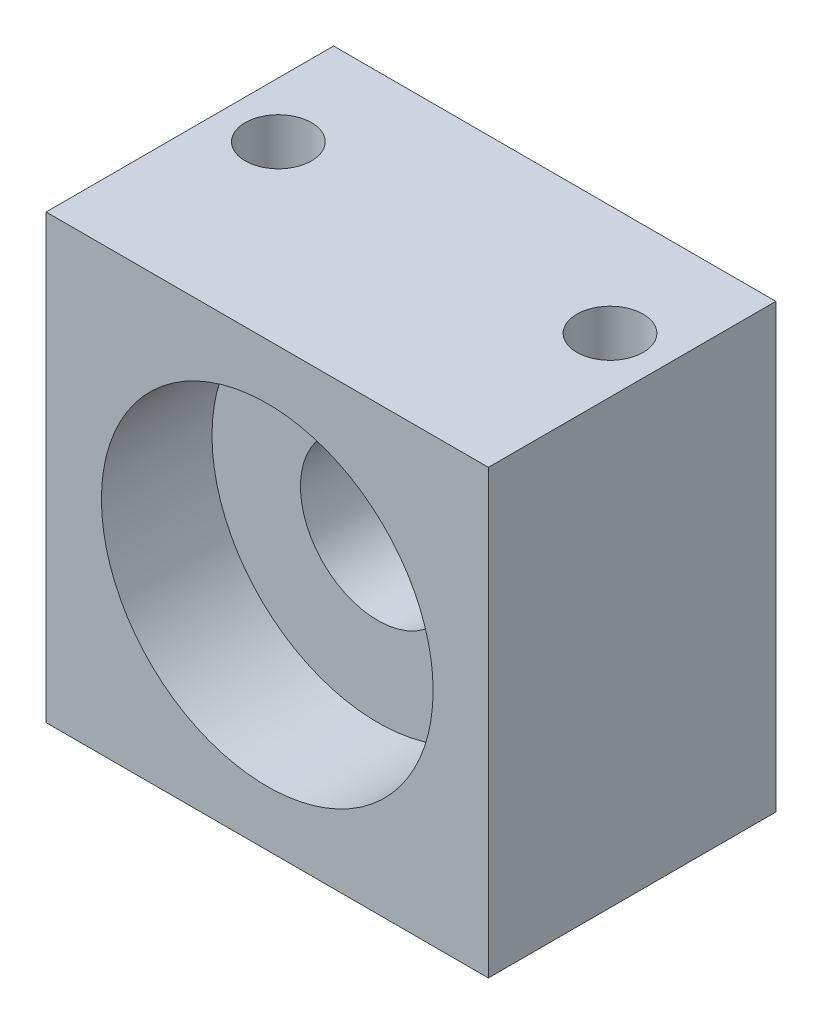
SolidWorks part; units mm, degrees
ref_plane "Front" through (0, 0, 0) normal (0, 0, 1) x (1, 0, 0)
ref_plane "Top" through (0, 0, 0) normal (0, 1, 0) x (1, 0, 0)
ref_plane "Right" through (0, 0, 0) normal (1, 0, 0) x (0, 0, -1)
sketch "Esquisse1" plane through (0, 0, 0) normal (0, 0, 1) x (1, 0, 0)
  line L1 (0, 0) -> (20, 0)
  line L2 (0, 0) -> (0, 20)
  line L3 (0, 20) -> (20, 20)
  line L4 (20, 0) -> (20, 20)
  dimension "D1" = 20
extrude "Boss.-Extru.1" add sketch "Esquisse1" along normal blind 13
sketch "Esquisse2" plane through (0, 0, 13) normal (0, 0, 1) x (1, 0, 0)
  line L0 (0, 20) -> (20, 0) construction
  circle A0 centre (10, 10) radius 7.5
  point P6 (0, 0)
  dimension "D1" = 15
extrude "Enlèv. mat.-Extru.1" cut sketch "Esquisse2" against normal blind 5
sketch "Esquisse3" plane through (0, 0, 8) normal (0, 0, 1) x (1, 0, 0)
  circle A0 centre (10, 10) radius 3.5
  circle A1 centre (10, 10) radius 7.5 construction
  dimension "D1" = 7
extrude "Enlèv. mat.-Extru.2" cut sketch "Esquisse3" against normal blind 5
sketch "Esquisse4" plane through (0, 20, 0) normal (0, 1, 0) x (1, 0, 0)
  line L0 (2.5, -5) -> (17.5, -5) construction
  line L1 (10, -5) -> (10, 0) construction
  line L2 (20, 0) -> (0, 0) construction
  circle A0 centre (2.5, -5) radius 1.5
  circle A1 centre (17.5, -5) radius 1.5
  dimension "D1" = 3
  dimension "D2" = 15
  dimension "D3" = 5
extrude "Enlèv. mat.-Extru.3" cut sketch "Esquisse4" against normal through all contours A1 | A0
